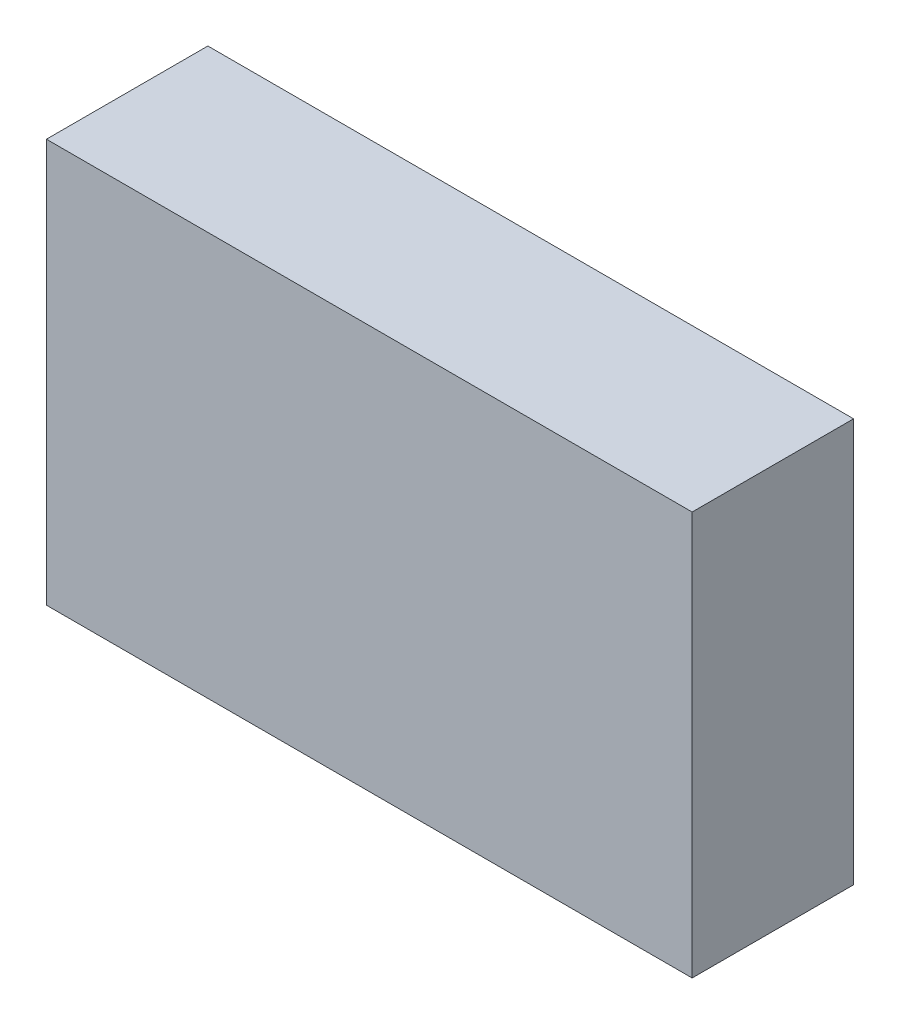
SolidWorks part; units mm, degrees
ref_plane "Front Plane" through (0, 0, 0) normal (0, 0, 1) x (1, 0, 0)
ref_plane "Top Plane" through (0, 0, 0) normal (0, 1, 0) x (1, 0, 0)
ref_plane "Right Plane" through (0, 0, 0) normal (1, 0, 0) x (0, 0, -1)
sketch "Sketch1" plane through (0, 0, 0) normal (0, 0, 1) x (1, 0, 0)
  line L1 (-37.0093, 20.8411) -> (42.9907, 20.8411)
  line L2 (-37.0093, 20.8411) -> (-37.0093, -29.1589)
  line L3 (-37.0093, -29.1589) -> (42.9907, -29.1589)
  line L4 (42.9907, 20.8411) -> (42.9907, -29.1589)
  dimension "D1" = 80
  dimension "D2" = 50
extrude "Boss-Extrude1" add sketch "Sketch1" along normal blind 20
